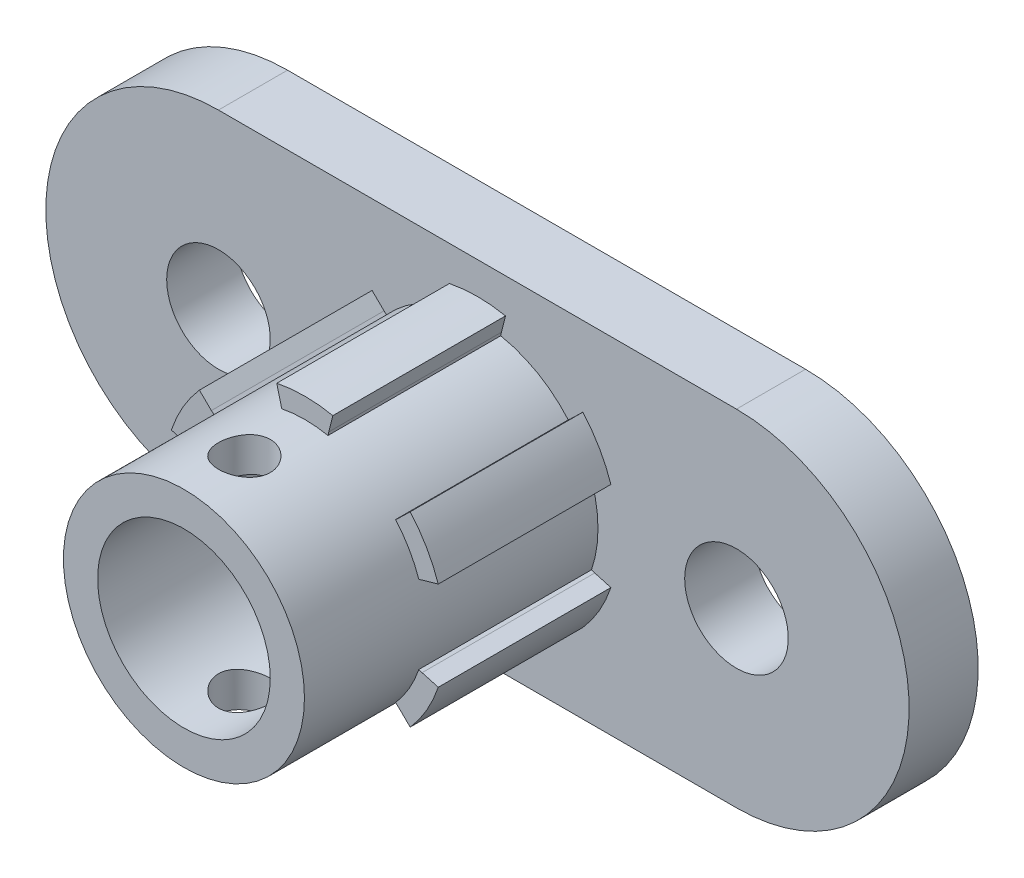
SolidWorks part; units mm, degrees
ref_plane "Front Plane" through (0, 0, 0) normal (0, 0, 1) x (1, 0, 0)
ref_plane "Top Plane" through (0, 0, 0) normal (0, 1, 0) x (1, 0, 0)
ref_plane "Right Plane" through (0, 0, 0) normal (1, 0, 0) x (0, 0, -1)
sketch "Sketch1" plane through (0, 0, 0) normal (0, 0, 1) x (1, 0, 0)
  point P0 (0, 0)
  point P1 (-7.58, 0)
  line B0 (1.8734, 7.3448) -> (2.1131, 8.2848)
  line B1 (-2.1131, 8.2848) -> (-1.8734, 7.3448)
  line B2 (-5.4241, 5.2948) -> (-6.1182, 5.9724)
  line B3 (-8.2314, 2.3123) -> (-7.2975, 2.05)
  line B4 (-7.2975, -2.05) -> (-8.2314, -2.3123)
  line B5 (-6.1182, -5.9724) -> (-5.4241, -5.2948)
  line B6 (-1.8734, -7.3448) -> (-2.1131, -8.2848)
  line B7 (2.1131, -8.2848) -> (1.8734, -7.3448)
  line B8 (5.4241, -5.2948) -> (6.1182, -5.9724)
  line B9 (8.2314, -2.3123) -> (7.2975, -2.05)
  line B10 (7.2975, 2.05) -> (8.2314, 2.3123)
  line B11 (6.1182, 5.9724) -> (5.4241, 5.2948)
  arc B12 (5.4241, 5.2948) -> (1.8734, 7.3448) centre (0, 0) ccw
  arc B13 (2.1131, 8.2848) -> (-2.1131, 8.2848) centre (0, 0) ccw
  arc B14 (-1.8734, 7.3448) -> (-5.4241, 5.2948) centre (0, 0) ccw
  arc B15 (-6.1182, 5.9724) -> (-8.2314, 2.3123) centre (0, 0) ccw
  arc B16 (-7.2975, 2.05) -> (-7.2975, -2.05) centre (0, 0) ccw
  arc B17 (-8.2314, -2.3123) -> (-6.1182, -5.9724) centre (0, 0) ccw
  arc B18 (-5.4241, -5.2948) -> (-1.8734, -7.3448) centre (0, 0) ccw
  arc B19 (-2.1131, -8.2848) -> (2.1131, -8.2848) centre (0, 0) ccw
  arc B20 (1.8734, -7.3448) -> (5.4241, -5.2948) centre (0, 0) ccw
  arc B21 (6.1182, -5.9724) -> (8.2314, -2.3123) centre (0, 0) ccw
  arc B22 (7.2975, -2.05) -> (7.2975, 2.05) centre (0, 0) ccw
  arc B23 (8.2314, 2.3123) -> (6.1182, 5.9724) centre (0, 0) ccw
  circle B24 centre (-15, 0) radius 2.5
  circle B25 centre (15, 0) radius 2.5
  dimension "D1" = 15
sketch_block_instance "Block2-1"
sketch_block "Block2"
sketch_block_instance "Block3-1"
sketch_block "Block3"
sketch "Sketch3" plane through (0, 0, 0) normal (0, 0, 1) x (1, 0, 0)
  line L24 (-7.7287, 2.5866) -> (-6.7935, 2.3239)
  line L25 (-5.4093, 4.7214) -> (-6.1044, 5.3999)
  line L26 (-6.7935, -2.3239) -> (-7.7287, -2.5866)
  line L27 (-1.3842, -7.0453) -> (-1.6243, -7.9865)
  line L28 (-6.1044, -5.3999) -> (-5.4093, -4.7214)
  line L29 (1.6243, -7.9865) -> (1.3842, -7.0453)
  line L30 (5.4093, -4.7214) -> (6.1044, -5.3999)
  line L31 (7.7287, -2.5866) -> (6.7935, -2.3239)
  line L32 (6.7935, 2.3239) -> (7.7287, 2.5866)
  line L33 (6.1044, 5.3999) -> (5.4093, 4.7214)
  line L34 (1.3842, 7.0453) -> (1.6243, 7.9865)
  line L35 (-1.6243, 7.9865) -> (-1.3842, 7.0453)
  line L36 (-7.7287, 2.5866) -> (-6.7935, 2.3239)
  line L37 (-5.4093, 4.7214) -> (-6.1044, 5.3999)
  line L38 (-6.7935, -2.3239) -> (-7.7287, -2.5866)
  line L39 (-1.3842, -7.0453) -> (-1.6243, -7.9865)
  line L40 (-6.1044, -5.3999) -> (-5.4093, -4.7214)
  line L41 (1.6243, -7.9865) -> (1.3842, -7.0453)
  line L42 (5.4093, -4.7214) -> (6.1044, -5.3999)
  line L43 (7.7287, -2.5866) -> (6.7935, -2.3239)
  line L44 (6.7935, 2.3239) -> (7.7287, 2.5866)
  line L45 (6.1044, 5.3999) -> (5.4093, 4.7214)
  line L46 (1.3842, 7.0453) -> (1.6243, 7.9865)
  line L47 (-1.6243, 7.9865) -> (-1.3842, 7.0453)
  arc A25 (-6.1044, 5.3999) -> (-7.7287, 2.5866) centre (0, 0) ccw
  arc A26 (-6.7935, 2.3239) -> (-6.7935, -2.3239) centre (0, 0) ccw
  arc A27 (-7.7287, -2.5866) -> (-6.1044, -5.3999) centre (0, 0) ccw
  arc A28 (-5.4093, -4.7214) -> (-1.3842, -7.0453) centre (0, 0) ccw
  arc A29 (-1.6243, -7.9865) -> (1.6243, -7.9865) centre (0, 0) ccw
  arc A30 (1.3842, -7.0453) -> (5.4093, -4.7214) centre (0, 0) ccw
  arc A31 (6.1044, -5.3999) -> (7.7287, -2.5866) centre (0, 0) ccw
  arc A32 (6.7935, -2.3239) -> (6.7935, 2.3239) centre (0, 0) ccw
  arc A33 (7.7287, 2.5866) -> (6.1044, 5.3999) centre (0, 0) ccw
  arc A34 (5.4093, 4.7214) -> (1.3842, 7.0453) centre (0, 0) ccw
  arc A35 (1.6243, 7.9865) -> (-1.6243, 7.9865) centre (0, 0) ccw
  arc A36 (-1.3842, 7.0453) -> (-5.4093, 4.7214) centre (0, 0) ccw
  arc A37 (-6.1044, 5.3999) -> (-7.7287, 2.5866) centre (0, 0) ccw
  arc A38 (-6.7935, 2.3239) -> (-6.7935, -2.3239) centre (0, 0) ccw
  arc A39 (-7.7287, -2.5866) -> (-6.1044, -5.3999) centre (0, 0) ccw
  arc A40 (-5.4093, -4.7214) -> (-1.3842, -7.0453) centre (0, 0) ccw
  arc A41 (-1.6243, -7.9865) -> (1.6243, -7.9865) centre (0, 0) ccw
  arc A42 (1.3842, -7.0453) -> (5.4093, -4.7214) centre (0, 0) ccw
  arc A43 (6.1044, -5.3999) -> (7.7287, -2.5866) centre (0, 0) ccw
  arc A44 (6.7935, -2.3239) -> (6.7935, 2.3239) centre (0, 0) ccw
  arc A45 (7.7287, 2.5866) -> (6.1044, 5.3999) centre (0, 0) ccw
  arc A46 (5.4093, 4.7214) -> (1.3842, 7.0453) centre (0, 0) ccw
  arc A47 (1.6243, 7.9865) -> (-1.6243, 7.9865) centre (0, 0) ccw
  arc A48 (-1.3842, 7.0453) -> (-5.4093, 4.7214) centre (0, 0) ccw
  dimension "D1" = 0.4
extrude "Boss-Extrude1" add sketch "Sketch3" along normal blind 10
sketch "Sketch4" plane through (0, 0, 0) normal (0, 0, -1) x (-1, 0, 0)
  line L0 (-15, 0) -> (15, 0) construction
  line L3 (-15, 0) -> (15, 0) construction
  line L4 (-15, 10) -> (15, 10)
  line L5 (-15, -10) -> (15, -10)
  circle A6 centre (-15, 0) radius 3
  circle A7 centre (15, 0) radius 3
  arc A8 (-15, 10) -> (-15, -10) centre (-15, 0) ccw
  arc A9 (15, -10) -> (15, 10) centre (15, 0) ccw
  point P0 (0, 0)
  point P4 (0, 0)
  dimension "D2" = 6
  dimension "D3" = 6
  dimension "D4" = 10
  dimension "D1" = 30
extrude "Boss-Extrude2" add sketch "Sketch4" along normal blind 4
sketch "Sketch8" plane through (0, 0, 10) normal (0, 0, 1) x (1, 0, 0)
  line L0 (-5.4093, 4.7214) -> (-5.2586, 4.5899)
  line L1 (-1.3842, 7.0453) -> (-1.3456, 6.8491)
  line L2 (5.4093, 4.7214) -> (5.2586, 4.5899)
  line L3 (1.3842, 7.0453) -> (1.3456, 6.8491)
  line L4 (6.7935, -2.3239) -> (6.6043, -2.2592)
  line L5 (6.7935, 2.3239) -> (6.6043, 2.2592)
  line L6 (1.3842, -7.0453) -> (1.3456, -6.8491)
  line L7 (5.4093, -4.7214) -> (5.2586, -4.5899)
  line L8 (-5.4093, -4.7214) -> (-5.2586, -4.5899)
  line L9 (-1.3842, -7.0453) -> (-1.3456, -6.8491)
  line L10 (-6.7935, 2.3239) -> (-6.6043, 2.2592)
  line L11 (-6.7935, -2.3239) -> (-6.6043, -2.2592)
  arc A0 (-1.3842, 7.0453) -> (-5.4093, 4.7214) centre (0, 0) ccw construction
  arc A1 (-1.3842, 7.0453) -> (-5.4093, 4.7214) centre (0, 0) ccw
  arc A2 (-1.3456, 6.8491) -> (-5.2586, 4.5899) centre (0, 0) ccw
  arc A3 (5.4093, 4.7214) -> (1.3842, 7.0453) centre (0, 0) ccw
  arc A4 (5.2586, 4.5899) -> (1.3456, 6.8491) centre (0, 0) ccw
  arc A5 (6.7935, -2.3239) -> (6.7935, 2.3239) centre (0, 0) ccw
  arc A6 (6.6043, -2.2592) -> (6.6043, 2.2592) centre (0, 0) ccw
  arc A7 (1.3842, -7.0453) -> (5.4093, -4.7214) centre (0, 0) ccw
  arc A8 (1.3456, -6.8491) -> (5.2586, -4.5899) centre (0, 0) ccw
  arc A9 (-5.4093, -4.7214) -> (-1.3842, -7.0453) centre (0, 0) ccw
  arc A10 (-5.2586, -4.5899) -> (-1.3456, -6.8491) centre (0, 0) ccw
  arc A11 (-6.7935, 2.3239) -> (-6.7935, -2.3239) centre (0, 0) ccw
  arc A12 (-6.6043, 2.2592) -> (-6.6043, -2.2592) centre (0, 0) ccw
  point P28 (0, 0)
  dimension "D1" = 0.2
  dimension "D2" = 6
extrude "Cut-Extrude2" cut sketch "Sketch8" against normal blind 10
sketch "Sketch9" plane through (0, 0, 10) normal (0, 0, 1) x (1, 0, 0)
  circle A0 centre (0, 0) radius 5
  dimension "D1" = 10
extrude "Cut-Extrude3" cut sketch "Sketch9" against normal through all
sketch "Sketch10" plane through (0, 0, 10) normal (0, 0, 1) x (1, 0, 0)
  circle A0 centre (0, 0) radius 5
  circle A1 centre (0, 0) radius 6.98
  dimension "D1" = 10
  dimension "D2" = 13.96
extrude "Boss-Extrude3" add sketch "Sketch10" along normal blind 7
sketch "Sketch11" plane through (0, 10, 0) normal (0, 1, 0) x (1, 0, 0)
  line L0 (-1.6243, -10) -> (1.6243, -10) construction
  circle A0 centre (0, -13.5) radius 1.5
  point P4 (0, 0)
  dimension "D1" = 3
  dimension "D2" = 3.5
extrude "Cut-Extrude4" cut sketch "Sketch11" against normal through all
